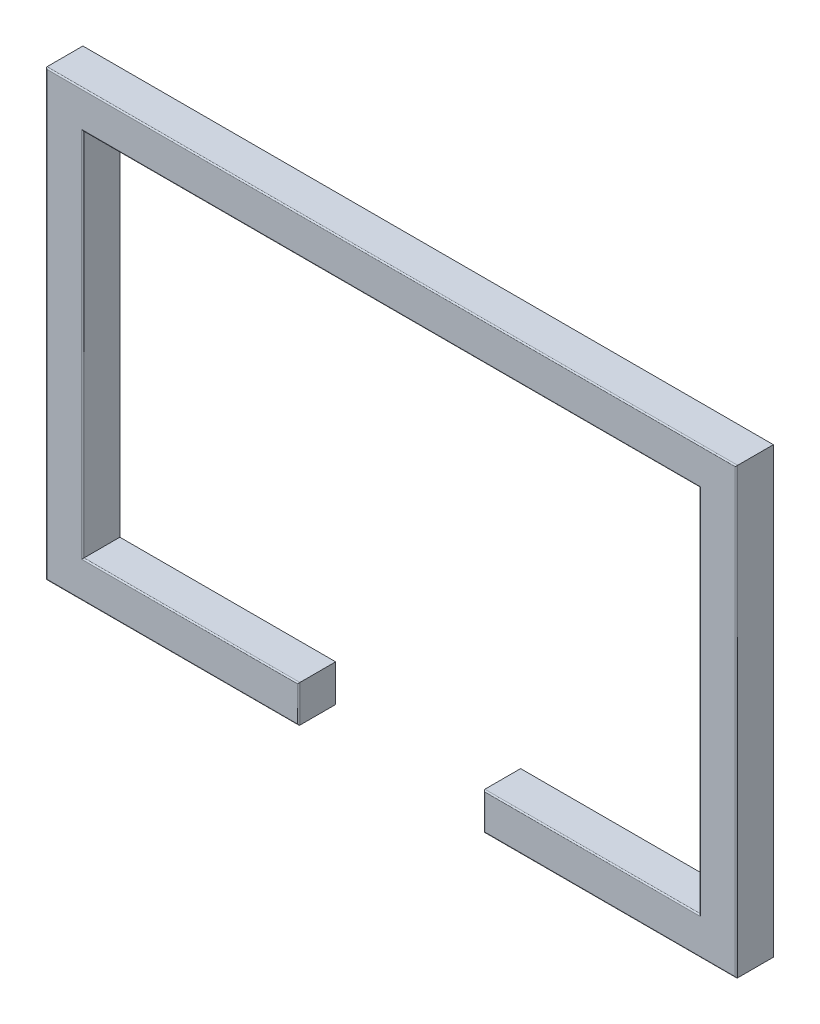
SolidWorks part; units mm, degrees
ref_plane "Front" through (0, 0, 0) normal (0, 0, 1) x (1, 0, 0)
ref_plane "Top" through (0, 0, 0) normal (0, 1, 0) x (1, 0, 0)
ref_plane "Right" through (0, 0, 0) normal (1, 0, 0) x (0, 0, -1)
sketch "Croquis1" plane through (0, 0, 0) normal (0, 0, 1) x (1, 0, 0)
  line L0 (-280, 180) -> (280, 180)
  line L1 (-250, 150) -> (250, 150)
  line L2 (-250, 150) -> (-250, -150)
  line L3 (-250, -150) -> (-75, -150)
  line L4 (250, 150) -> (250, -150)
  line L5 (-250, 150) -> (250, -150) construction
  line L6 (-250, -150) -> (250, 150) construction
  line L7 (280, 180) -> (280, -180)
  line L8 (-280, -180) -> (-75, -180)
  line L9 (-280, 180) -> (-280, -180)
  line L10 (-75, -180) -> (-75, -150)
  line L11 (75, -180) -> (75, -150)
  line L12 (75, -180) -> (280, -180)
  line L13 (-280, -180) -> (280, -180) construction
  line L14 (75, -150) -> (250, -150)
  line L15 (-250, -150) -> (250, -150) construction
  point P0 (0, 0)
  dimension "D1" = 500
  dimension "D2" = 300
  dimension "D4" = 75
  dimension "D5" = 75
  dimension "D3" = 30
extrude "Saliente-Extruir1" add sketch "Croquis1" along normal blind 30
fillet "Redondeo1" radius 1 12 edges at (-75, -165, 30) (-162.5, -150, 30) (-250, 0, 30) (0, 150, 30) (250, 0, 30) (162.5, -150, 30) (75, -165, 30) (280, 0, 30) (177.5, -180, 30) (-177.5, -180, 30) (-280, 0, 30) (0, 180, 30)
